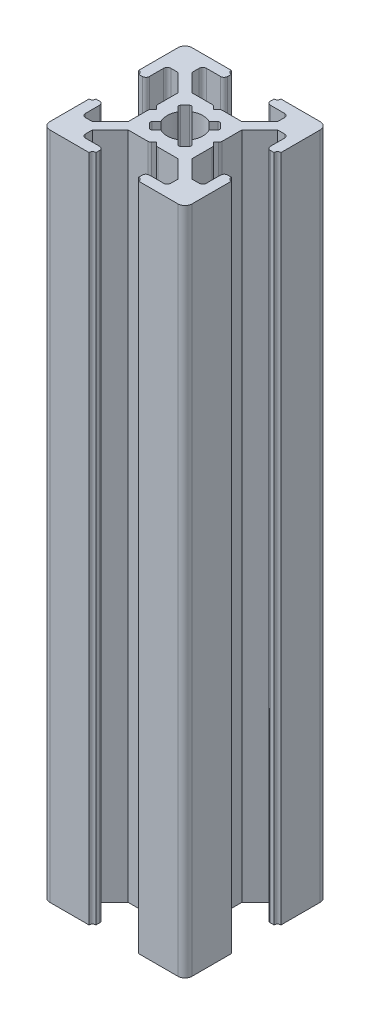
SolidWorks part; units mm, degrees
ref_plane "Front Plane" through (0, 0, 0) normal (0, 0, 1) x (1, 0, 0)
ref_plane "Top Plane" through (0, 0, 0) normal (0, 1, 0) x (1, 0, 0)
ref_plane "Right Plane" through (0, 0, 0) normal (1, 0, 0) x (0, 0, -1)
sketch "Sketch3" plane through (0, 0, 0) normal (0, 1, 0) x (1, 0, 0)
  line L0 (7, 20) -> (7, 18.5)
  line L1 (0, 0) -> (20, 0)
  line L2 (0, 0) -> (0, 20)
  line L3 (0, 20) -> (20, 20)
  line L4 (20, 0) -> (20, 20)
  line L5 (7, 18.5) -> (4, 18.5)
  line L6 (4, 18.5) -> (4, 17)
  line L7 (4, 17) -> (6.5, 14.5)
  line L8 (6.5, 14.5) -> (13.5, 14.5)
  line L9 (13.5, 14.5) -> (16, 17)
  line L10 (16, 17) -> (16, 18.5)
  line L11 (16, 18.5) -> (13, 18.5)
  line L12 (13, 18.5) -> (13, 20)
  line L13 (13, 20) -> (7, 20)
  line L14 (9.5, 14.5) -> (10, 14)
  line L15 (10, 14) -> (10.5, 14.5)
  line L16 (10.5, 14.5) -> (9.5, 14.5)
  line L17 (13, 19.5) -> (13, 20)
  line L18 (13.5, 20) -> (13, 20)
  line L19 (7, 19.5) -> (7, 20)
  line L20 (6.5, 20) -> (7, 20)
  line L21 (0, 13) -> (1.5, 13)
  line L22 (1.5, 13) -> (1.5, 16)
  line L23 (1.5, 16) -> (3, 16)
  line L24 (3, 16) -> (5.5, 13.5)
  line L25 (5.5, 13.5) -> (5.5, 6.5)
  line L26 (5.5, 6.5) -> (3, 4)
  line L27 (3, 4) -> (1.5, 4)
  line L28 (1.5, 4) -> (1.5, 7)
  line L29 (1.5, 7) -> (0, 7)
  line L30 (0, 7) -> (0, 13)
  line L31 (5.5, 10.5) -> (5.5, 9.5)
  line L32 (5.5, 9.5) -> (6, 10)
  line L33 (6, 10) -> (5.5, 10.5)
  line L34 (0.5, 13) -> (0, 13)
  line L35 (0, 13.5) -> (0, 13)
  line L36 (0, 6.5) -> (0, 7)
  line L37 (0.5, 7) -> (0, 7)
  line L38 (10, 20) -> (10, 0) construction
  line L39 (20, 10) -> (0, 10) construction
  line L40 (10, 6) -> (10.5, 5.5)
  line L41 (9.5, 5.5) -> (10, 6)
  line L42 (10.5, 5.5) -> (9.5, 5.5)
  line L43 (13.5, 0) -> (13, 0)
  line L44 (13, 0.5) -> (13, 0)
  line L45 (6.5, 0) -> (7, 0)
  line L46 (7, 0.5) -> (7, 0)
  line L47 (13, 1.5) -> (13, 0)
  line L48 (16, 1.5) -> (13, 1.5)
  line L49 (16, 3) -> (16, 1.5)
  line L50 (13.5, 5.5) -> (16, 3)
  line L51 (6.5, 5.5) -> (13.5, 5.5)
  line L52 (4, 3) -> (6.5, 5.5)
  line L53 (4, 1.5) -> (4, 3)
  line L54 (7, 1.5) -> (4, 1.5)
  line L55 (7, 0) -> (7, 1.5)
  line L56 (13, 0) -> (7, 0)
  line L57 (14.5, 9.5) -> (14, 10)
  line L58 (14.5, 10.5) -> (14.5, 9.5)
  line L59 (14, 10) -> (14.5, 10.5)
  line L60 (19.5, 7) -> (20, 7)
  line L61 (20, 6.5) -> (20, 7)
  line L62 (20, 13.5) -> (20, 13)
  line L63 (19.5, 13) -> (20, 13)
  line L64 (18.5, 7) -> (20, 7)
  line L65 (18.5, 4) -> (18.5, 7)
  line L66 (17, 4) -> (18.5, 4)
  line L67 (14.5, 6.5) -> (17, 4)
  line L68 (14.5, 13.5) -> (14.5, 6.5)
  line L69 (17, 16) -> (14.5, 13.5)
  line L70 (18.5, 16) -> (17, 16)
  line L71 (18.5, 13) -> (18.5, 16)
  line L72 (20, 13) -> (18.5, 13)
  line L73 (20, 7) -> (20, 13)
  arc A0 (13.5, 20) -> (13, 19.5) centre (13, 20) cw
  arc A1 (6.5, 20) -> (7, 19.5) centre (7, 20) ccw
  arc A2 (0.5, 13) -> (0, 13.5) centre (0, 13) ccw
  arc A3 (0.5, 7) -> (0, 6.5) centre (0, 7) cw
  arc A4 (13.5, 0) -> (13, 0.5) centre (13, 0) ccw
  arc A5 (6.5, 0) -> (7, 0.5) centre (7, 0) cw
  arc A6 (19.5, 7) -> (20, 6.5) centre (20, 7) ccw
  arc A7 (19.5, 13) -> (20, 13.5) centre (20, 13) cw
  point P7 (10, 14.5)
  point P16 (10, 20)
  point P26 (5.5, 10)
  point P35 (0, 10)
  dimension "D16" = 0.5
  dimension "D17" = 0.5
  dimension "D28" = 0.5
  dimension "D29" = 0.5
  dimension "D1" = 20
  dimension "D2" = 20
  dimension "D3" = 7
  dimension "D4" = 7
  dimension "D5" = 1.5
  dimension "D6" = 1.5
  dimension "D7" = 3
  dimension "D8" = 3
  dimension "D9" = 1.5
  dimension "D10" = 1.5
  dimension "D11" = 7
  dimension "D12" = 5.5
  dimension "D13" = 0.5
  dimension "D14" = 0.5
  dimension "D15" = 0.5
  dimension "D18" = 7
  dimension "D19" = 7
  dimension "D20" = 1.5
  dimension "D21" = 1.5
  dimension "D22" = 3
  dimension "D23" = 7
  dimension "D24" = 5.5
  dimension "D25" = 0.5
  dimension "D26" = 0.5
  dimension "D27" = 0.5
extrude "Boss-Extrude1" add sketch "Sketch3" along normal blind 94 contours L72 A7 L4 L3 A0 L12 L11 L10 L9 L8 L15 L14 L7 L6 L5 L0 A1 L2 A2 L21 L22 L23 L24 L25 L33 L32 L26 L27 L28 L29 A3 L1 A5 L55 L54 L53 L52 L51 L41 L40 L50 L49 L48 L47 A4
fillet "Fillet1" radius 1 4 edges at (0, 47, 0) (20, 47, 0) (20, 47, -20) (0, 47, -20)
sketch "Sketch4" plane through (0, 94, 0) normal (0, 1, 0) x (1, 0, 0)
  line L0 (13.5, 14.5) -> (5.5, 6.5) construction
  line L1 (14.5, 13.5) -> (6.5, 5.5) construction
  line L2 (10.5, 14.5) -> (14.5, 10.5) construction
  line L3 (12, 13) -> (13, 12)
  line L4 (13, 12) -> (8, 7)
  line L5 (8, 7) -> (7, 8)
  line L6 (7, 8) -> (12, 13)
  line L7 (13.5, 14.5) -> (16, 17) construction
  line L8 (17, 16) -> (14.5, 13.5) construction
  line L9 (5.5, 9.5) -> (9.5, 5.5) construction
  line L10 (5.5, 10.5) -> (9.5, 14.5) construction
  line L11 (14.5, 9.5) -> (10.5, 5.5) construction
  line L12 (6.5, 14.5) -> (14.5, 6.5) construction
  line L13 (5.5, 13.5) -> (13.5, 5.5) construction
  line L14 (7, 12) -> (8, 13)
  line L15 (8, 13) -> (13, 8)
  line L16 (13, 8) -> (12, 7)
  line L17 (12, 7) -> (7, 12)
  line L18 (4, 17) -> (6.5, 14.5) construction
  line L19 (3, 16) -> (5.5, 13.5) construction
  line L20 (20, 10) -> (0, 10) construction
  circle A0 centre (10, 10) radius 2.5
  dimension "D1" = 5
extrude "Cut-Extrude1" cut sketch "Sketch4" against normal through all contours L6 A0 L15 | L4 A0 L6 L15 | L15 A0 L17 L6 | L17 L4 L15 L6 | L17 A0 L6 | L6 A0 L4 L17 | L4 A0 L17 | L17 A0 L15 L4 | L15 A0 L4 | A0 L6 L5 L4 | A0 L17 L16 L15 | A0 L4 L3 L6 | A0 L15 L14 L17
fillet "Fillet2" radius 0.5 24 edges at (1.5, 47, -16) (1.5, 47, -13) (5.5, 47, -10.5) (5.5, 47, -9.5) (1.5, 47, -7) (1.5, 47, -4) (4, 47, -1.5) (7, 47, -1.5) (9.5, 47, -5.5) (10.5, 47, -5.5) (13, 47, -1.5) (16, 47, -1.5) (18.5, 47, -4) (18.5, 47, -7) (18.5, 47, -13) (18.5, 47, -16) (14.5, 47, -9.5) (14.5, 47, -10.5) (10.5, 47, -14.5) (9.5, 47, -14.5) (16, 47, -18.5) (13, 47, -18.5) (7, 47, -18.5) (4, 47, -18.5)
fillet "Fillet3" radius 0.25 8 edges at (13, 47, -8) (12, 47, -7) (13, 47, -12) (12, 47, -13) (8, 47, -13) (7, 47, -12) (7, 47, -8) (8, 47, -7)
